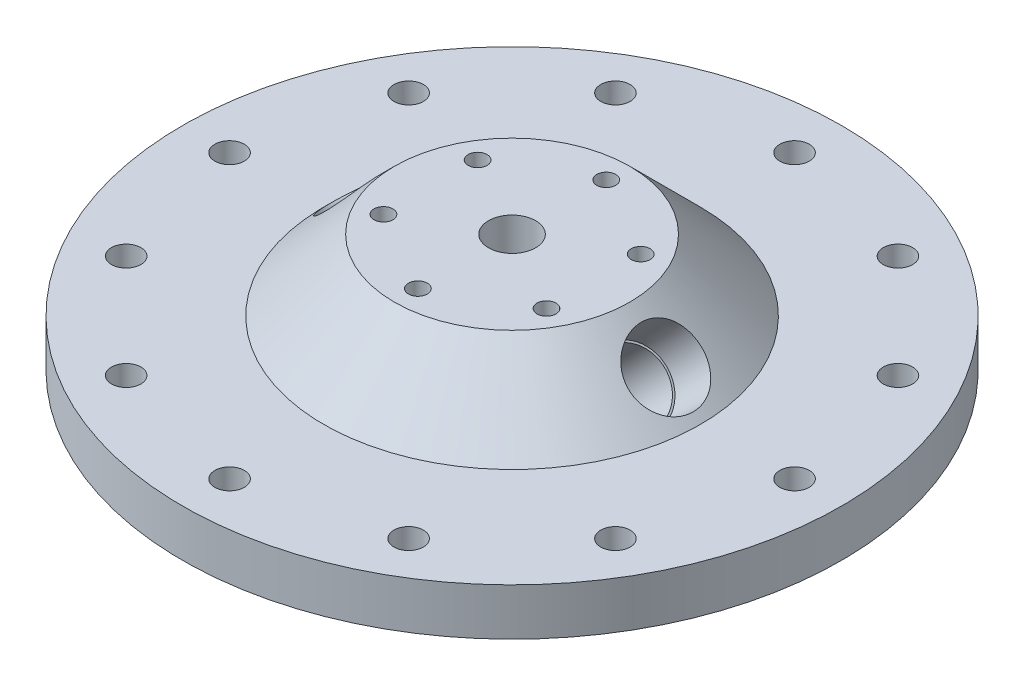
SolidWorks part; units mm, degrees
ref_plane "Front Plane" through (0, 0, 0) normal (0, 0, 1) x (1, 0, 0)
ref_plane "Top Plane" through (0, 0, 0) normal (0, 1, 0) x (1, 0, 0)
ref_plane "Right Plane" through (0, 0, 0) normal (1, 0, 0) x (0, 0, -1)
sketch "Sketch1" plane through (0, 0, 0) normal (0, 0, 1) x (1, 0, 0)
  line L0 (-6.35, 0) -> (-88.9, 0)
  line L1 (-88.9, 0) -> (-88.9, 12.7)
  line L2 (-88.9, 12.7) -> (-50.8, 12.7)
  line L3 (-6.35, 31.75) -> (-6.35, 0)
  line L6 (0, 0) -> (0, 8.9137) construction
  line L7 (-50.8, 12.7) -> (-31.75, 31.75)
  line L8 (-31.75, 31.75) -> (-6.35, 31.75)
  point P5 (-24.5074, 21.7779)
  point P8 (-6.35, 21.6079)
  dimension "D1" = 6.35
  dimension "D2" = 88.9
  dimension "D3" = 12.7
  dimension "D4" = 45
  dimension "D5" = 31.75
  dimension "D6" = 19.05
revolve "Revolve1" add sketch "Sketch1" angle 360 about L6
hole_wizard "5/16 (0.3125) Diameter Hole1" positions "Sketch2" profile "Sketch3" hole size "5/16" standard "ANSI Inch"
sketch "Sketch2" plane through (0, 12.7, 0) normal (0, 1, 0) x (1, 0, 0)
  point P0 (76.2, 0)
  point P4 (0, 0)
  dimension "D1" = 76.2
sketch "Sketch3" plane through (76.2, 12.7, 0) normal (1, 0, 0) x (0, 0, 1)
  line L0 (0, 0) -> (0, 31.0867)
  line L1 (0, 31.0867) -> (3.9687, 28.702)
  line L2 (3.9687, 28.702) -> (3.9687, 0)
  line L5 (3.9687, 0) -> (0, 0)
  line L10 (0, 31.0867) -> (-3.9688, 28.702) construction
  line L11 (0, -6.35) -> (0, 107.95) construction
  dimension "Hole Dia." = 7.9375
  dimension "Hole Depth" = 28.702
  dimension "Drill Angle" = 118
pattern_circular "CirPattern1" count 12 over 360 about axis through (0, 0, 0) along (0, 1, 0) of "5/16 (0.3125) Diameter Hole1"
ref_plane "Plane1" through (31.75, 31.75, 0) normal (0.7071, 0.7071, 0) x (0, 0, -1)
ref_plane "Plane2" through (-31.75, 31.75, 0) normal (-0.7071, 0.7071, 0) x (0, 0, 1)
hole_wizard "1/2 NPT Tapped Hole1" positions "Sketch4" profile "Sketch5" size "1/2" standard "ANSI Inch"
sketch "Sketch4" plane through (31.75, 31.75, 0) normal (0.7071, 0.7071, 0) x (0, 0, -1)
  point P0 (0, -14.2875)
  point P4 (0, 0)
  dimension "D1" = 14.2875
sketch "Sketch5" plane through (41.8528, 21.6472, 0) normal (0, 0, 1) x (-0.7071, 0.7071, 0)
  line L0 (0, 0) -> (0, 33.9395)
  line L1 (8.9281, 28.575) -> (0, 33.9395)
  line L2 (-8.9281, 28.575) -> (0, 33.9395) construction
  line L3 (8.9281, 28.575) -> (8.9281, 13.462)
  line L4 (8.9281, 13.462) -> (9.4797, 13.462)
  line L5 (9.4797, 13.462) -> (9.8828, 0)
  line L6 (-9.4797, 13.462) -> (-9.8828, 0) construction
  line L7 (9.8828, 0) -> (0, 0)
  line L8 (0, -6.35) -> (0, 107.95) construction
  line L11 (-8.9281, 13.462) -> (-9.4797, 13.462) construction
  dimension "Tap Drill Dia." = 17.8562
  dimension "Tap Drill Depth" = 28.575
  dimension "Thread Dia." = 19.7656
  dimension "Thread Angle" = 3.43
  dimension "Thread Depth" = 13.462
  dimension "Drill Angle" = 118
cosmetic thread "Hole Thread1" parameters "D1"=13.462, "D2"=21.3295
hole_wizard "1/2 NPT Tapped Hole2" positions "Sketch6" profile "Sketch7" size "1/2" standard "ANSI Inch"
sketch "Sketch6" plane through (-31.75, 31.75, 0) normal (-0.7071, 0.7071, 0) x (0, 0, 1)
  point P0 (0, -14.2875)
  point P3 (0, 0)
  dimension "D1" = 14.2875
sketch "Sketch7" plane through (-41.8528, 21.6472, 0) normal (0, 0, 1) x (-0.7071, -0.7071, 0)
  line L0 (0, 0) -> (0, 34.0665)
  line L1 (8.9281, 28.702) -> (0, 34.0665)
  line L2 (-8.9281, 28.702) -> (0, 34.0665) construction
  line L3 (8.9281, 28.702) -> (8.9281, 13.462)
  line L4 (8.9281, 13.462) -> (9.4797, 13.462)
  line L5 (9.4797, 13.462) -> (9.8828, 0)
  line L6 (-9.4797, 13.462) -> (-9.8828, 0) construction
  line L7 (9.8828, 0) -> (0, 0)
  line L8 (0, -6.35) -> (0, 107.95) construction
  line L11 (-8.9281, 13.462) -> (-9.4797, 13.462) construction
  dimension "Tap Drill Dia." = 17.8562
  dimension "Tap Drill Depth" = 28.702
  dimension "Thread Dia." = 19.7656
  dimension "Thread Angle" = 3.43
  dimension "Thread Depth" = 13.462
  dimension "Drill Angle" = 118
cosmetic thread "Hole Thread2" parameters "D1"=13.462, "D2"=21.3295
hole_wizard "1/4-20 Tapped Hole1" positions "Sketch8" profile "Sketch9" tap size "1/4-20" standard "ANSI Inch"
sketch "Sketch8" plane through (0, 31.75, 0) normal (0, 1, 0) x (1, 0, 0)
  line L0 (0, 0) -> (21.997, 12.7) construction
  line L2 (0, 0) -> (18.8645, 0) construction
  point P0 (21.997, 12.7)
  dimension "D1" = 30
  dimension "D2" = 25.4
sketch "Sketch9" plane through (21.997, 31.75, -12.7) normal (1, 0, 0) x (0, 0, 1)
  line L0 (0, 0) -> (0, 18.0438)
  line L1 (0, 18.0438) -> (2.5527, 16.51)
  line L2 (2.5527, 16.51) -> (2.5527, 0)
  line L5 (2.5527, 0) -> (0, 0)
  line L10 (0, 18.0438) -> (-2.5527, 16.51) construction
  line L11 (0, -6.35) -> (0, 107.95) construction
  dimension "Tap Drill Dia." = 5.1054
  dimension "Tap Drill Depth" = 16.51
  dimension "Drill Angle" = 118
cosmetic thread "Hole Thread3" parameters "D1"=12.7, "D2"=6.35
pattern_circular "CirPattern2" count 6 over 360 about axis through (0, 0, 0) along (0, 1, 0) of "1/4-20 Tapped Hole1"
cosmetic thread "Hole Thread4" parameters "D1"=12.7, "D2"=6.35
cosmetic thread "Hole Thread5" parameters "D1"=12.7, "D2"=6.35
cosmetic thread "Hole Thread6" parameters "D1"=12.7, "D2"=6.35
cosmetic thread "Hole Thread7" parameters "D1"=12.7, "D2"=6.35
cosmetic thread "Hole Thread8" parameters "D1"=12.7, "D2"=6.35
hole_wizard "1/8 (0.125) Diameter Hole1" positions "Sketch10" profile "Sketch11" hole size "1/8" standard "ANSI Inch"
sketch "Sketch10" plane through (0, 0, 0) normal (0, -1, 0) x (-1, 0, 0)
  line L0 (0, 0) -> (35.7452, -20.6375) construction
  line L2 (38.5519, 0) -> (0, 0) construction
  point P0 (35.7452, -20.6375)
  dimension "D1" = 41.275
  dimension "D2" = 30
sketch "Sketch11" plane through (-35.7452, 0, 20.6375) normal (1, 0, 0) x (0, 0, -1)
  line L0 (0, 0) -> (0, 4.1289)
  line L1 (0, 4.1289) -> (1.5875, 3.175)
  line L2 (1.5875, 3.175) -> (1.5875, 0)
  line L5 (1.5875, 0) -> (0, 0)
  line L10 (0, 4.1289) -> (-1.5875, 3.175) construction
  line L11 (0, -6.35) -> (0, 107.95) construction
  dimension "Hole Dia." = 3.175
  dimension "Hole Depth" = 3.175
  dimension "Drill Angle" = 118
